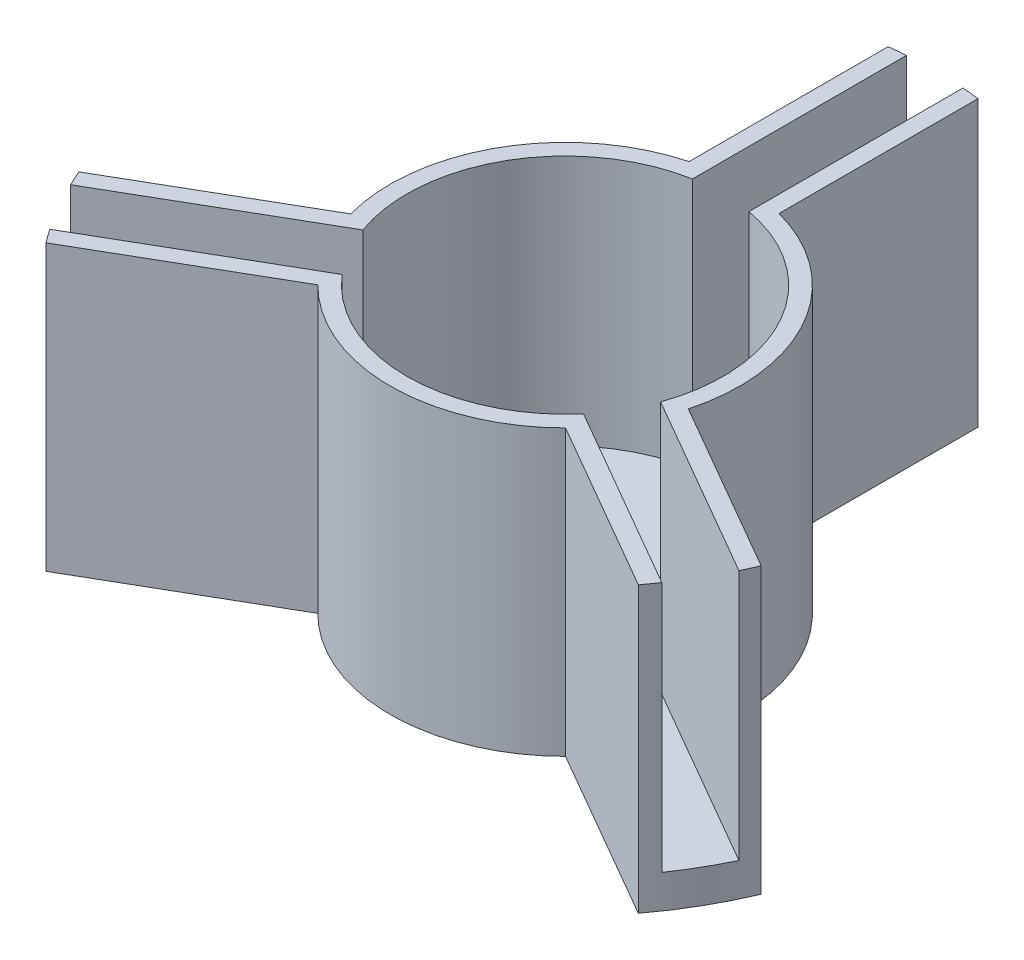
SolidWorks part; units mm, degrees
other "Markup1"
sketch "Sketch5" plane through (34.95, 15, 34.95) normal (0.0371, 0.9957, 0.0854) x (0.9174, 0, -0.3981)
ref_plane "Front Plane" through (0, 0, 0) normal (0, 0, 1) x (1, 0, 0)
ref_plane "Top Plane" through (0, 0, 0) normal (0, 1, 0) x (1, 0, 0)
ref_plane "Right Plane" through (0, 0, 0) normal (1, 0, 0) x (0, 0, -1)
sketch "Sketch2" plane through (0, 0, 0) normal (0, 1, 0) x (1, 0, 0)
  circle A0 centre (0, 0) radius 9.45
  circle A1 centre (0, 0) radius 22.15
  dimension "D1" = 18.9
  dimension "D2" = 12.7
extrude "Boss-Extrude2" add sketch "Sketch2" along normal blind 15 contours A1 A0
sketch "Sketch3" plane through (0, 0, 0) normal (0, -1, 0) x (1, 0, 0)
  circle A0 centre (0, 0) radius 22.15 construction
  circle A1 centre (0, 0) radius 22.15
extrude "Boss-Extrude3" add sketch "Sketch3" along normal blind 2
sketch "Sketch4" plane through (0, 15, 0) normal (0, 1, 0) x (1, 0, 0)
  line L0 (-1.6875, 22.0856) -> (-1.6875, 9.2981)
  line L1 (1.6875, 9.2981) -> (1.6875, 22.0856)
  line L2 (0, 0) -> (0, 24.9078) construction
  line L3 (-1.6875, 36.1723) -> (1.6875, 36.1723) construction
  circle A0 centre (0, 0) radius 22.15 construction
  circle A1 centre (0, 0) radius 9.45 construction
  arc A2 (1.6875, 22.0856) -> (-1.6875, 22.0856) centre (0, 0) ccw
  arc A3 (1.6875, 9.2981) -> (-1.6875, 9.2981) centre (0, 0) ccw
  arc A4 (-1.6875, 22.0856) -> (1.6875, 22.0856) centre (0, 0) ccw construction
  arc A5 (-1.6875, 9.2981) -> (1.6875, 9.2981) centre (0, 0) ccw construction
  point P11 (0, 36.1723)
  dimension "D1" = 3.375
extrude "Cut-Extrude1" cut sketch "Sketch4" against normal up to surface (15 mm away) up to face at (0, 0, 9.45)
pattern_circular "CirPattern1" count 3 over 360 about axis through (0, 0, 0) along (0, 1, 0) of "Cut-Extrude1"
sketch "Sketch6" plane through (0, 15, 0) normal (0, 1, 0) x (1, 0, 0)
  line L0 (-20.3845, -8.6657) -> (-10.0893, -2.7218)
  line L1 (-8.8961, -3.1876) -> (-19.9705, -9.5814) construction
  line L2 (-2.6875, 21.9864) -> (-2.6875, 10.0985)
  line L3 (-1.6875, 22.0856) -> (-1.6875, 9.2981) construction
  arc A0 (-1.6875, 22.0856) -> (-19.9705, -9.5814) centre (0, 0) ccw construction
  arc A1 (-2.6875, 21.9864) -> (-20.3845, -8.6657) centre (0, 0) ccw
  arc A2 (-2.6875, 10.0985) -> (-10.0893, -2.7218) centre (0, 0) ccw
  arc A3 (-1.6875, 9.2981) -> (-8.8961, -3.1876) centre (0, 0) ccw construction
  arc A4 (-10.0893, -2.7218) -> (-2.6875, 10.0985) centre (0, 0) ccw construction
  dimension "D3" = 1
  dimension "D1" = 1
  dimension "D2" = 1
extrude "Cut-Extrude2" cut sketch "Sketch6" against normal up to surface (17 mm away) up to face at (0, -2, -22.15)
pattern_circular "CirPattern2" count 3 over 360 about axis through (0, 0, 0) along (0, 1, 0) of "Cut-Extrude2"
equation "\"B_OD\" = 18.7mm"
equation "\"B_ID\" = 18mm"
equation "\"B_LG\" = 9in"
equation "\"F_TH\" = 0.125in"
equation "\"C_TH\" = 0.125in"
equation "\"fins\" = 3"
equation "\"D1@Sketch2\"=\"B_OD\" + \"tol\""
equation "\"tol\" = 0.2mm"
equation "\"D1@Sketch4\"=\"F_TH\"+\"tol\""
equation "\"D1@CirPattern1\"=\"fins\""
equation "\"D1@CirPattern2\"=\"fins\""
